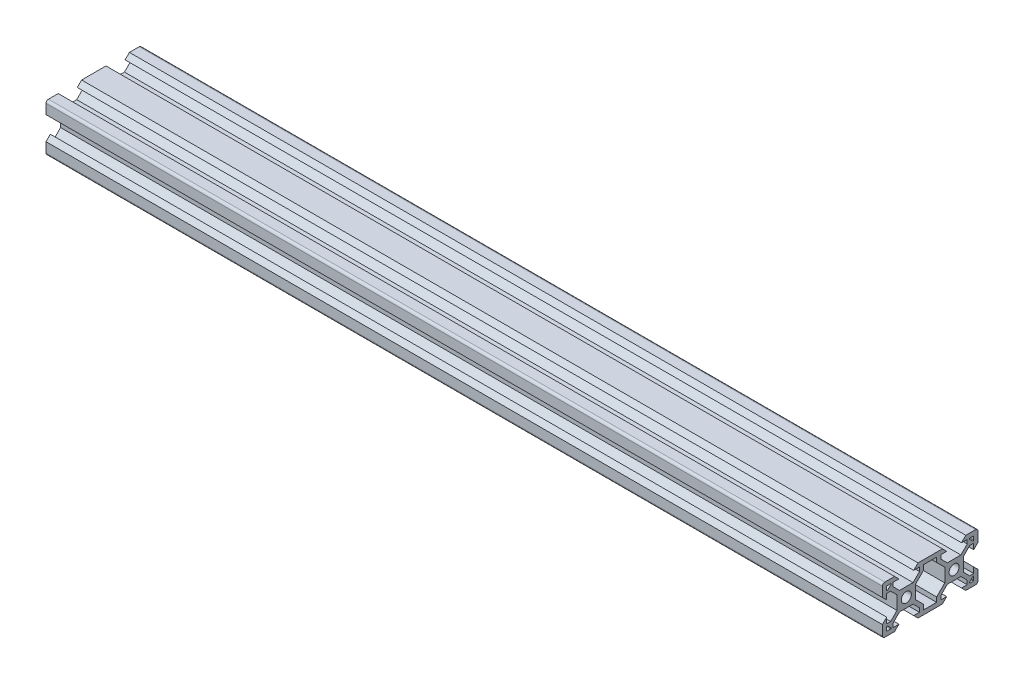
SolidWorks part; units mm, degrees
material "1060 Alloy"
ref_plane "Front Plane" through (0, 0, 0) normal (0, 0, 1) x (1, 0, 0)
ref_plane "Top Plane" through (0, 0, 0) normal (0, 1, 0) x (1, 0, 0)
ref_plane "Right Plane" through (0, 0, 0) normal (1, 0, 0) x (0, 0, -1)
sketch "Sketch4" plane through (0, 0, 0) normal (1, 0, 0) x (0, 0, -1)
  line L0 (-19.2399, 7.0114) -> (20.7601, 7.0114) construction
  dimension "D1" = 40
sketch "Sketch5" plane through (0, 0, 0) normal (1, 0, 0) x (0, 0, -1)
  line L0 (-19.998, 4.9) -> (-18.198, 3.1)
  line L1 (-18.198, 3.1) -> (-18.198, 5.4993)
  line L2 (-18.198, 5.4993) -> (-16.558, 5.4993)
  line L3 (-16.558, 5.4993) -> (-13.9, 2.8413)
  line L4 (-13.9, 2.8413) -> (-13.9, -2.8387)
  line L5 (-13.9, -2.8387) -> (-16.558, -5.4967)
  line L6 (-16.558, -5.4967) -> (-18.198, -5.4967)
  line L7 (-18.198, -5.4967) -> (-18.198, -3.1)
  line L8 (-18.198, -3.1) -> (-19.998, -4.9)
  line L9 (-19.998, -4.9) -> (-19.998, -9)
  line L10 (-18.998, -10) -> (-14.9, -10)
  line L11 (-14.9, -10) -> (-13.1, -8.2)
  line L12 (-13.1, -8.2) -> (-15.5, -8.2)
  line L13 (-15.5, -8.2) -> (-15.5, -6.56)
  line L14 (-15.5, -6.56) -> (-12.84, -3.9)
  line L15 (-12.84, -3.9) -> (-7.16, -3.9)
  line L16 (-7.16, -3.9) -> (-4.5, -6.56)
  line L17 (-4.5, -6.56) -> (-4.5, -8.2)
  line L18 (-4.5, -8.2) -> (-6.9, -8.2)
  line L19 (-6.9, -8.2) -> (-5.1, -10)
  line L20 (-5.1, -10) -> (5.1, -10)
  line L21 (5.1, -10) -> (6.9, -8.2)
  line L22 (6.9, -8.2) -> (4.496, -8.2)
  line L23 (4.496, -8.2) -> (4.496, -6.56)
  line L24 (4.496, -6.56) -> (7.156, -3.9)
  line L25 (7.156, -3.9) -> (12.836, -3.9)
  line L26 (12.836, -3.9) -> (15.496, -6.56)
  line L27 (15.496, -6.56) -> (15.496, -8.2)
  line L28 (15.496, -8.2) -> (13.1, -8.2)
  line L29 (13.1, -8.2) -> (14.9, -10)
  line L30 (14.9, -10) -> (19.002, -10)
  line L31 (20.002, -9) -> (20.002, -4.9)
  line L32 (20.002, -4.9) -> (18.202, -3.1)
  line L33 (18.202, -3.1) -> (18.202, -5.5046)
  line L34 (18.202, -5.5046) -> (16.562, -5.5046)
  line L35 (16.562, -5.5046) -> (13.9, -2.8426)
  line L36 (13.9, -2.8426) -> (13.9, 2.8374)
  line L37 (13.9, 2.8374) -> (16.562, 5.4993)
  line L38 (16.562, 5.4993) -> (18.202, 5.4993)
  line L39 (18.202, 5.4993) -> (18.202, 3.1)
  line L40 (18.202, 3.1) -> (20.002, 4.9)
  line L41 (20.002, 4.9) -> (20.002, 9)
  line L42 (19.002, 10) -> (14.9, 10)
  line L43 (14.9, 10) -> (13.1, 8.2)
  line L44 (13.1, 8.2) -> (15.5013, 8.2)
  line L45 (15.5013, 8.2) -> (15.5013, 6.56)
  line L46 (15.5013, 6.56) -> (12.8413, 3.9)
  line L47 (12.8413, 3.9) -> (7.1613, 3.9)
  line L48 (7.1613, 3.9) -> (4.5013, 6.56)
  line L49 (4.5013, 6.56) -> (4.5013, 8.2)
  line L50 (4.5013, 8.2) -> (6.9, 8.2)
  line L51 (6.9, 8.2) -> (5.1, 10)
  line L52 (5.1, 10) -> (-5.1, 10)
  line L53 (-5.1, 10) -> (-6.9, 8.2)
  line L54 (-6.9, 8.2) -> (-4.5013, 8.2)
  line L55 (-4.5013, 8.2) -> (-4.5013, 6.56)
  line L56 (-4.5013, 6.56) -> (-7.1613, 3.9)
  line L57 (-7.1613, 3.9) -> (-12.8413, 3.9)
  line L58 (-12.8413, 3.9) -> (-15.5013, 6.56)
  line L59 (-15.5013, 6.56) -> (-15.5013, 8.2)
  line L60 (-15.5013, 8.2) -> (-13.1, 8.2)
  line L61 (-13.1, 8.2) -> (-14.9, 10)
  line L62 (-14.9, 10) -> (-18.998, 10)
  line L63 (-19.998, 9) -> (-19.998, 4.9)
  line L64 (6.1, -2.84) -> (6.1, 2.84)
  line L65 (6.1, 2.84) -> (2.7, 6.24)
  line L66 (2.7, 6.24) -> (2.7, 8.2)
  line L67 (2.7, 8.2) -> (-2.7, 8.2)
  line L68 (-2.7, 8.2) -> (-2.7, 6.24)
  line L69 (-2.7, 6.24) -> (-6.1, 2.84)
  line L70 (-6.1, 2.84) -> (-6.1, -2.84)
  line L71 (-6.1, -2.84) -> (-2.7, -6.24)
  line L72 (-2.7, -6.24) -> (-2.7, -8.2)
  line L73 (-2.7, -8.2) -> (2.7, -8.2)
  line L74 (2.7, -8.2) -> (2.7, -6.24)
  line L75 (2.7, -6.24) -> (6.1, -2.84)
  line L76 (0, -8.2) -> (0, 8.2) construction
  line L77 (6.1, 0) -> (-6.1, 0) construction
  line L78 (16.562, 5.4993) -> (15.5013, 6.56) construction
  line L79 (16.5713, 8.2) -> (18.002, 8.2)
  line L81 (17.8606, 6.4279) -> (16.4299, 7.8586)
  line L82 (18.202, 8) -> (18.202, 6.5693)
  line L83 (18.002, 6.5693) -> (18.002, 8) construction
  line L84 (18.002, 8) -> (16.5713, 8) construction
  line L85 (16.5713, 8) -> (18.002, 6.5693) construction
  line L86 (16.5713, -8.2) -> (18.002, -8.2)
  line L87 (18.202, -8) -> (18.202, -6.5693)
  line L88 (17.8606, -6.4279) -> (16.4299, -7.8586)
  line L89 (-17.8606, 6.4279) -> (-16.4299, 7.8586)
  line L90 (-16.5713, 8.2) -> (-18.002, 8.2)
  line L91 (-18.202, 8) -> (-18.202, 6.5693)
  line L92 (-16.5713, -8.2) -> (-18.002, -8.2)
  line L93 (-17.8606, -6.4279) -> (-16.4299, -7.8586)
  line L94 (-18.202, -8) -> (-18.202, -6.5693)
  circle A0 centre (-10, 0) radius 2.1
  circle A1 centre (10, 0) radius 2.1
  arc A2 (-19.998, -9) -> (-18.998, -10) centre (-18.998, -9) ccw
  arc A5 (-18.998, 10) -> (-19.998, 9) centre (-18.998, 9) ccw
  arc A6 (20.002, -9) -> (19.002, -10) centre (19.002, -9) cw
  arc A7 (20.002, 9) -> (19.002, 10) centre (19.002, 9) ccw
  arc A8 (18.002, 8.2) -> (18.202, 8) centre (18.002, 8) cw
  arc A10 (16.4299, 7.8586) -> (16.5713, 8.2) centre (16.5713, 8) cw
  arc A12 (18.202, 6.5693) -> (17.8606, 6.4279) centre (18.002, 6.5693) cw
  arc A13 (16.4299, -7.8586) -> (16.5713, -8.2) centre (16.5713, -8) ccw
  arc A14 (18.002, -8.2) -> (18.202, -8) centre (18.002, -8) ccw
  arc A15 (18.202, -6.5693) -> (17.8606, -6.4279) centre (18.002, -6.5693) ccw
  arc A16 (-18.202, 6.5693) -> (-17.8606, 6.4279) centre (-18.002, 6.5693) ccw
  arc A17 (-16.4299, 7.8586) -> (-16.5713, 8.2) centre (-16.5713, 8) ccw
  arc A18 (-18.002, 8.2) -> (-18.202, 8) centre (-18.002, 8) ccw
  arc A19 (-18.002, -8.2) -> (-18.202, -8) centre (-18.002, -8) cw
  arc A20 (-16.4299, -7.8586) -> (-16.5713, -8.2) centre (-16.5713, -8) cw
  arc A21 (-18.202, -6.5693) -> (-17.8606, -6.4279) centre (-18.002, -6.5693) cw
  dimension "D1" = 4.2
  dimension "D20" = 3.9
  dimension "D27" = 1
  dimension "D40" = 1
  dimension "D41" = 1
  dimension "D42" = 1
  dimension "D45" = 0.2
  dimension "D47" = 1.07
  dimension "D48" = 1.07
  dimension "D49" = 0.2
  dimension "D2" = 20
  dimension "D3" = 10
  dimension "D4" = 5.68
  dimension "D5" = 5.4
  dimension "D6" = 1.96
  dimension "D7" = 45
  dimension "D8" = 1.8
  dimension "D9" = 1.64
  dimension "D10" = 1.8
  dimension "D11" = 40
  dimension "D12" = 20
  dimension "D13" = 3.9
  dimension "D14" = 1.5
  dimension "D15" = 1.5
  dimension "D16" = 3.9
  dimension "D17" = 3.9
  dimension "D18" = 3.9
  dimension "D19" = 3.9
  dimension "D21" = 1.5
  dimension "D22" = 1.5
  dimension "D23" = 1.64
  dimension "D24" = 45
  dimension "D25" = 1.5
  dimension "D26" = 1.8
  dimension "D28" = 6.2
  dimension "D29" = 6.2
  dimension "D30" = 6.2
  dimension "D31" = 6.2
  dimension "D32" = 6.2
  dimension "D33" = 3.1
  dimension "D34" = 3.1
  dimension "D35" = 3.1
  dimension "D36" = 3.1
  dimension "D37" = 6.2
  dimension "D38" = 3.1
  dimension "D39" = 3.1
  dimension "D43" = 1.64
  dimension "D44" = 135
  dimension "D46" = 45
extrude "Boss-Extrude1" add sketch "Sketch5" along normal mid plane 350
